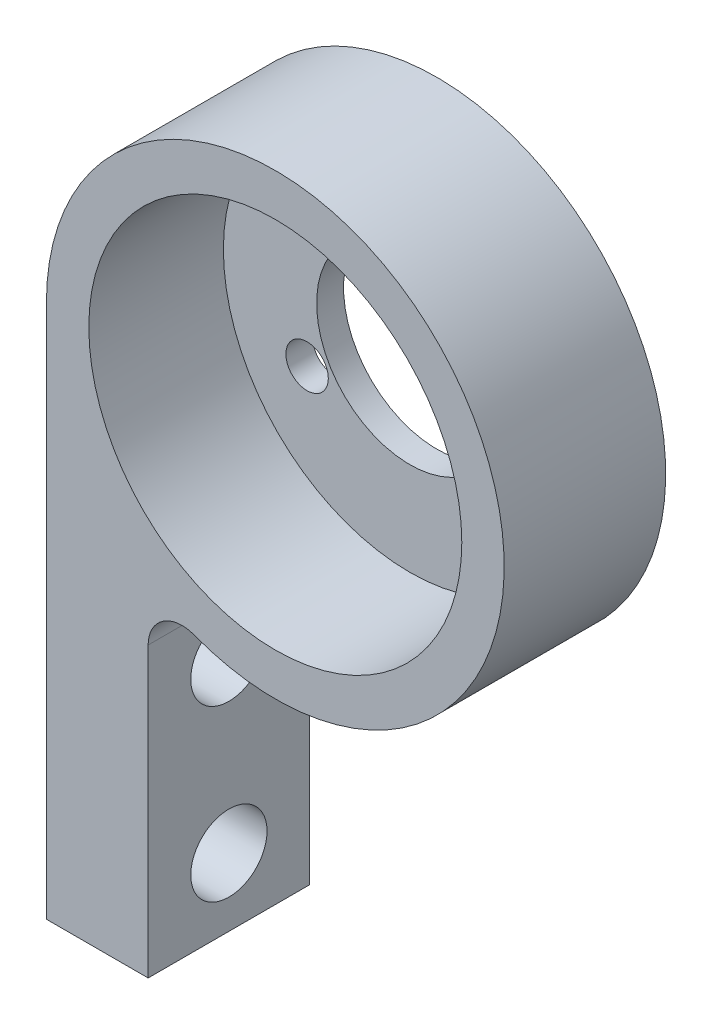
SolidWorks part; units mm, degrees
material "6061-T6 (SS)"
ref_plane "Front Plane" through (0, 0, 0) normal (0, 0, 1) x (1, 0, 0)
ref_plane "Top Plane" through (0, 0, 0) normal (0, 1, 0) x (1, 0, 0)
ref_plane "Right Plane" through (0, 0, 0) normal (1, 0, 0) x (0, 0, -1)
sketch "Sketch2" plane through (0, 0, 0) normal (0, 0, 1) x (1, 0, 0)
  line L1 (3, -15.75) -> (-3, -15.75)
  line L2 (3, -15.75) -> (3, 15.75)
  line L3 (3, 15.75) -> (-3, 15.75)
  line L4 (-3, -15.75) -> (-3, 15.75)
  line L5 (3, -15.75) -> (-3, 15.75) construction
  line L6 (3, 15.75) -> (-3, -15.75) construction
  circle A0 centre (10.5, 15.75) radius 13.5
  circle A1 centre (10.5, 15.75) radius 5.5
  point P0 (0, 0)
  dimension "D3" = 27
  dimension "D4" = 11
  dimension "D1" = 6
  dimension "D2" = 31.5
  dimension "D5" = 31.5
  dimension "D6" = 13.5
extrude "Boss-Extrude1" add sketch "Sketch2" along normal mid plane 9.525 contours A0 L4 L1 L2 | A1 L4 A0 L2 | A1 L2 A0 L4
hole_wizard "M4 Clearance Hole1" positions "Sketch3" profile "Sketch4" hole size "M4" standard "ANSI Metric" end condition through all
sketch "Sketch3" plane through (3, 0, 0) normal (1, 0, 0) x (0, 0, -1)
  line L0 (-4.7625, -15.75) -> (4.7625, -15.75) construction
  point P0 (0, -1.75)
  point P2 (0, -11.75)
  dimension "D1" = 10
  dimension "D2" = 4
sketch "Sketch4" plane through (3, -1.75, 0) normal (0, 1, 0) x (0, 0, -1)
  line L0 (0, 0) -> (0, 6)
  line L1 (0, 6) -> (2.25, 6)
  line L2 (2.25, 6) -> (2.25, 0)
  line L5 (2.25, 0) -> (0, 0)
  line L11 (0, -6.35) -> (0, 107.95) construction
  dimension "Thru Hole Dia." = 4.5
  dimension "Thru Hole Depth" = 6
fillet "Fillet1" radius 2 1 edges at (3, 4.525, 0)
sketch "Sketch5" plane through (0, 0, 4.7625) normal (0, 0, 1) x (1, 0, 0)
  circle A0 centre (10.5, 15.75) radius 11
  dimension "D1" = 22
extrude "Cut-Extrude1" cut sketch "Sketch5" against normal blind 7.9375
hole_wizard "M3x0.5 Tapped Hole1" positions "Sketch6" profile "Sketch7" tap size "M3x0.5" standard "ANSI Metric" end condition through all
sketch "Sketch6" plane through (0, 0, -4.7625) normal (0, 0, -1) x (-1, 0, 0)
  point P0 (-10.5, 22.75)
  point P2 (-16.5622, 12.25)
  point P4 (-4.4378, 12.25)
sketch "Sketch7" plane through (10.5, 22.75, -4.7625) normal (1, 0, 0) x (0, 1, 0)
  line L0 (0, 0) -> (0, 9.525)
  line L1 (0, 9.525) -> (1.25, 9.525)
  line L2 (1.25, 9.525) -> (1.25, 0)
  line L5 (1.25, 0) -> (0, 0)
  line L11 (0, -6.35) -> (0, 107.95) construction
  dimension "Thru Tap Drill Dia." = 2.5
  dimension "Thru Tap Drill Depth" = 9.525
cosmetic thread "Hole Thread1" parameters "D2"=3
cosmetic thread "Hole Thread2" parameters "D2"=3
cosmetic thread "Hole Thread3" parameters "D2"=3
